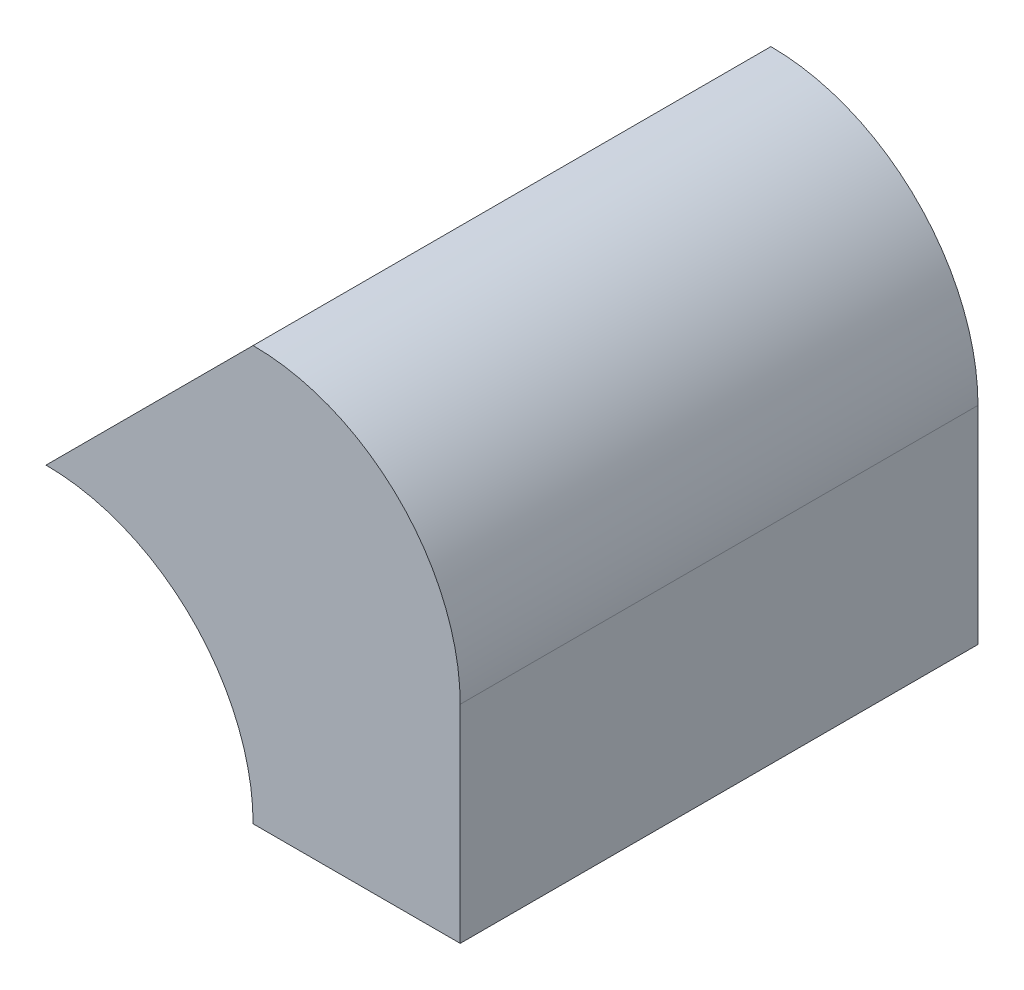
SolidWorks part; units mm, degrees
ref_plane "Front Plane" through (0, 0, 0) normal (0, 0, 1) x (1, 0, 0)
ref_plane "Top Plane" through (0, 0, 0) normal (0, 1, 0) x (1, 0, 0)
ref_plane "Right Plane" through (0, 0, 0) normal (1, 0, 0) x (0, 0, -1)
sketch "Sketch1" plane through (0, 0, 0) normal (0, 0, 1) x (1, 0, 0)
  line L0 (-10, 0) -> (0, 0)
  line L1 (0, 0) -> (0, 10)
  line L2 (-20, 10) -> (-10, 20)
  arc A0 (0, 10) -> (-10, 20) centre (-10, 10) ccw
  arc A1 (-10, 0) -> (-20, 10) centre (-20, 0) ccw
  dimension "D1" = 10
  dimension "D2" = 10
extrude "Boss-Extrude1" add sketch "Sketch1" along normal blind 25
